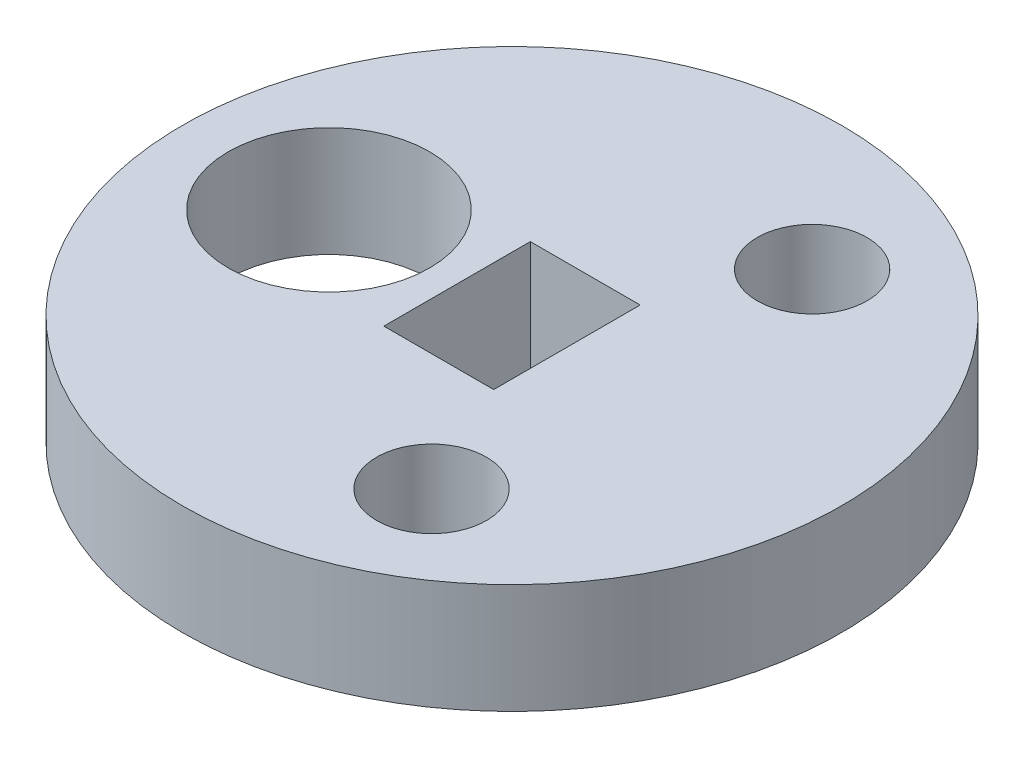
SolidWorks part; units mm, degrees
ref_plane "Front Plane" through (0, 0, 0) normal (0, 0, 1) x (1, 0, 0)
ref_plane "Top Plane" through (0, 0, 0) normal (0, 1, 0) x (1, 0, 0)
ref_plane "Right Plane" through (0, 0, 0) normal (1, 0, 0) x (0, 0, -1)
sketch "Sketch1" plane through (0, 0, 0) normal (0, 1, 0) x (1, 0, 0)
  line L1 (-1.5, 2) -> (-1.5, -2)
  line L2 (1.5, 2) -> (1.5, -2)
  line L3 (-1.5, -2) -> (1.5, -2)
  line L4 (-1.5, 2) -> (1.5, 2)
  circle A1 centre (-5, 0.0008) radius 2.75
  circle A2 centre (0, 0) radius 9
  circle A3 centre (2.9991, -5.1967) radius 1.5
  circle A4 centre (3.0009, 5.1957) radius 1.5
  dimension "D1" = 18
  dimension "D3" = 5.5
  dimension "D4" = 6
  dimension "D7" = 3
  dimension "D8" = 3
  dimension "D2" = 5
  dimension "D5" = 4
  dimension "D6" = 6
extrude "Boss-Extrude1" add sketch "Sketch1" along normal blind 3
